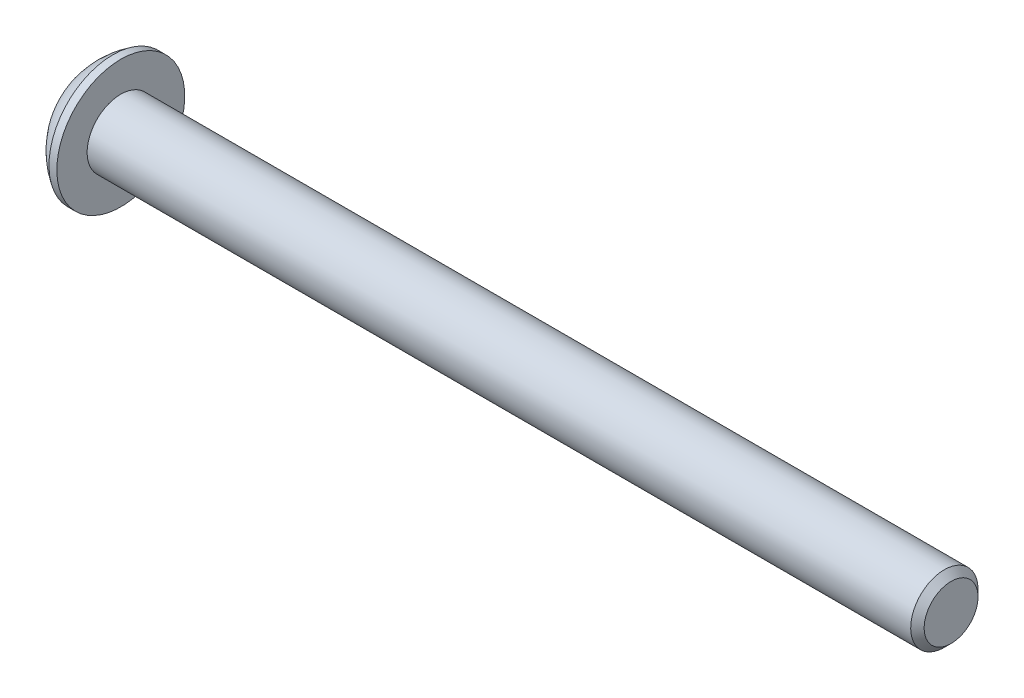
SolidWorks part; units mm, degrees
ref_plane "Front Plane" through (0, 0, 0) normal (0, 0, 1) x (1, 0, 0)
ref_plane "Top Plane" through (0, 0, 0) normal (0, 1, 0) x (1, 0, 0)
ref_plane "Right Plane" through (0, 0, 0) normal (1, 0, 0) x (0, 0, -1)
sketch "Sketch1" plane through (0, 0, 0) normal (0, 0, 1) x (1, 0, 0)
  line L0 (38.65, 0) -> (0, 0)
  line L1 (0, 0) -> (0, 1.425)
  line L2 (1.3, 2.85) -> (1.65, 2.85)
  line L3 (1.65, 2.85) -> (1.65, 1.5)
  line L4 (1.65, 1.5) -> (38.65, 1.5)
  line L5 (38.65, 1.5) -> (38.65, 0)
  arc A1 (1.3, 2.85) -> (0, 1.425) centre (3.1356, -0.13) ccw
  point P3 (1.65, 2.175)
  dimension "D6" = 3.5
  dimension "D1" = 37
  dimension "D2" = 1.5
  dimension "D3" = 2.85
  dimension "D4" = 0.35
  dimension "D5" = 1.65
  dimension "D7" = 1.425
revolve "Revolve1" add sketch "Sketch1" angle 360 about L0
chamfer "Chamfer1" distance 0.3 angle 45 1 edges at (38.65, 1.5, 0)
sketch "Sketch2" plane through (0, 0, 0) normal (-1, 0, 0) x (0, 0, 1)
  line L1 (0, 1.1547) -> (-1, 0.5774)
  line L2 (-1, 0.5774) -> (-1, -0.5774)
  line L3 (-1, -0.5774) -> (0, -1.1547)
  line L4 (0, -1.1547) -> (1, -0.5774)
  line L5 (1, -0.5774) -> (1, 0.5774)
  line L6 (1, 0.5774) -> (0, 1.1547)
  circle A0 centre (0, 0) radius 1 construction
  dimension "D1" = 2
extrude "Cut-Extrude1" cut sketch "Sketch2" against normal blind 1
scale "Scale1" scale about centroid uniform scaling yes scale factor 1.667
